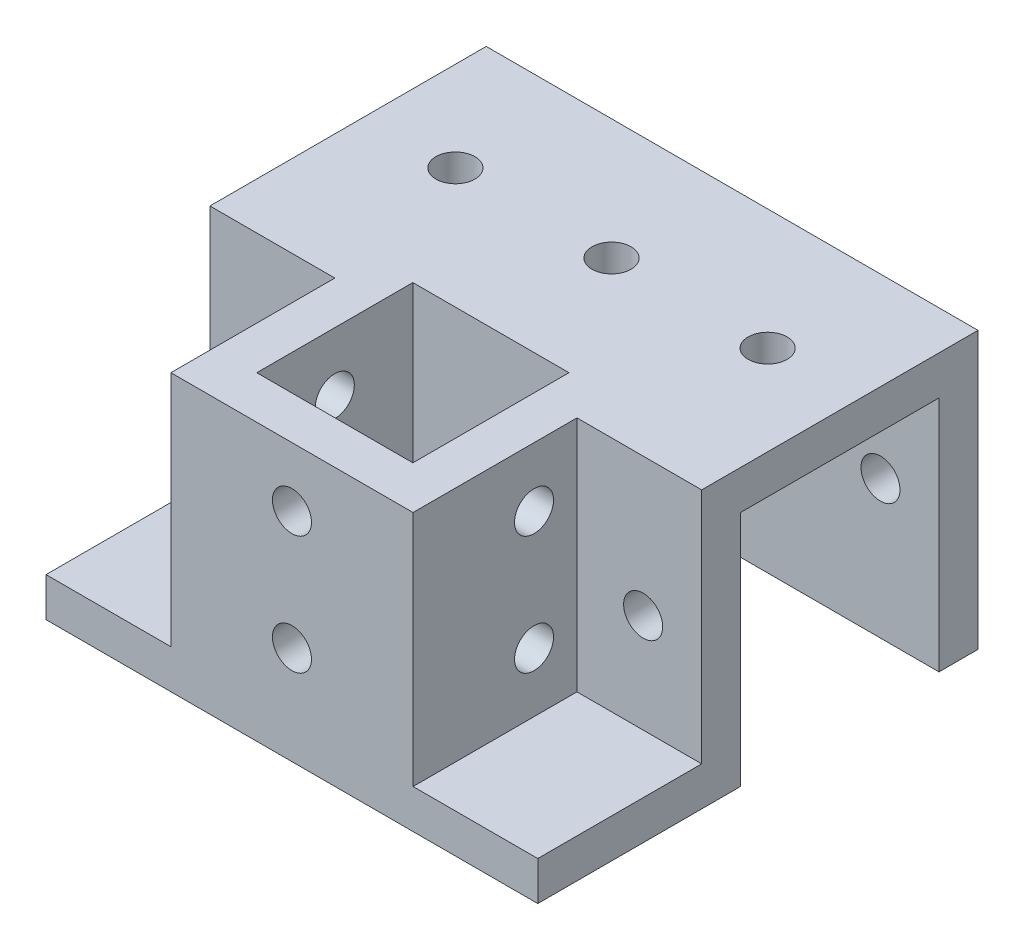
SolidWorks part; units mm, degrees
material "PLA"
ref_plane "Front Plane" through (0, 0, 0) normal (0, 0, 1) x (1, 0, 0)
ref_plane "Top Plane" through (0, 0, 0) normal (0, 1, 0) x (1, 0, 0)
ref_plane "Right Plane" through (0, 0, 0) normal (1, 0, 0) x (0, 0, -1)
sketch "Sketch2" plane through (0, 0, 0) normal (1, 0, 0) x (0, 0, -1)
  line L0 (-17.7, 17.7) -> (17.7, 17.7)
  line L1 (-12.7, 12.7) -> (12.7, 12.7)
  line L2 (-12.7, 12.7) -> (-12.7, -12.7)
  line L4 (12.7, 12.7) -> (12.7, -12.7)
  line L5 (-12.7, 12.7) -> (12.7, -12.7) construction
  line L6 (-12.7, -12.7) -> (12.7, 12.7) construction
  line L7 (17.7, 17.7) -> (17.7, -17.7)
  line L9 (-17.7, 17.7) -> (-17.7, -17.7)
  line L10 (-17.7, -17.7) -> (17.7, -17.7) construction
  line L11 (12.7, -12.7) -> (12.7, -17.7)
  line L12 (12.7, -17.7) -> (17.7, -17.7)
  line L13 (-12.7, -12.7) -> (-12.7, -17.7)
  line L14 (-12.7, -17.7) -> (-17.7, -17.7)
  line L16 (-12.7, -12.7) -> (12.7, -12.7) construction
  point P0 (0, 0)
  dimension "D1" = 25.4
  dimension "D2" = 25.4
  dimension "D3" = 5
extrude "Boss-Extrude1" add sketch "Sketch2" along normal blind 21
sketch "Sketch4" plane through (0, 0, 17.7) normal (0, 0, 1) x (1, 0, 0)
  line L0 (21, -17.7) -> (21, -12.7)
  line L1 (21, 17.7) -> (21, -17.7) construction
  line L2 (21, -12.7) -> (-21, -12.7)
  line L3 (21, -17.7) -> (-21, -17.7)
  line L4 (-21, -17.7) -> (-21, -12.7)
  dimension "D1" = 42
  dimension "D2" = 5
extrude "Boss-Extrude2" add sketch "Sketch4" along normal blind 21
sketch "Sketch5" plane through (0, 0, 17.7) normal (0, 0, -1) x (-1, 0, 0)
  line L0 (0, -17.7) -> (0, -12.7)
  line L1 (0, -12.7) -> (21, -12.7)
  line L2 (21, -12.7) -> (21, -17.7)
  line L3 (21, -17.7) -> (0, -17.7)
extrude "Boss-Extrude3" add sketch "Sketch5" along normal blind 5
sketch "Sketch7" plane through (0, 0, 17.7) normal (0, 0, 1) x (1, 0, 0)
  line L0 (0, 17.7) -> (5.0226, 17.7)
  line L1 (21, 17.7) -> (0, 17.7) construction
  line L2 (5.0226, 17.7) -> (5.0226, -12.7)
  line L3 (21, -12.7) -> (-21, -12.7) construction
  line L4 (5.0226, -12.7) -> (0, -12.7)
  line L5 (0, 17.7) -> (0, -12.7)
extrude "Boss-Extrude4" add sketch "Sketch7" along normal up to surface (21 mm away) up to face at (0, -15.2, 38.7)
sketch "Sketch8" plane through (-21, 0, 0) normal (-1, 0, 0) x (0, 0, 1)
  line L0 (12.7, -17.7) -> (12.7, 17.7)
  line L1 (-17.7, 17.7) -> (38.7, 17.7) construction
  line L2 (12.7, 17.7) -> (38.7, 17.7)
  line L3 (38.7, 17.7) -> (38.7, -17.7)
  line L4 (38.7, -17.7) -> (12.7, -17.7)
extrude "Boss-Extrude5" add sketch "Sketch8" along normal blind 5
sketch "Sketch9" plane through (-26, 0, 0) normal (-1, 0, 0) x (0, 0, 1)
  line L0 (12.7, -17.7) -> (12.7, -12.7)
  line L1 (12.7, 17.7) -> (12.7, -17.7) construction
  line L2 (12.7, -12.7) -> (38.7, -12.7)
  line L3 (38.7, -17.7) -> (38.7, 17.7) construction
  line L4 (38.7, -12.7) -> (38.7, -17.7)
  line L5 (38.7, -17.7) -> (12.7, -17.7)
  dimension "D1" = 5
extrude "Boss-Extrude6" add sketch "Sketch9" along normal blind 16 contours L5 L0 L2 L4
sketch "Sketch10" plane through (0, 0, 12.7) normal (0, 0, -1) x (-1, 0, 0)
  line L0 (26, 17.7) -> (42, 17.7)
  line L1 (26, 17.7) -> (26, -12.7)
  line L2 (42, -12.7) -> (42, 17.7)
  line L3 (26, -12.7) -> (42, -12.7)
extrude "Boss-Extrude7" add sketch "Sketch10" against normal blind 5 contours L3 L2 L0 L1
sketch "Sketch11" plane through (0, 0, 12.7) normal (0, 0, -1) x (-1, 0, 0)
  line L0 (21, 17.7) -> (21, 12.7)
  line L1 (21, 17.7) -> (21, -12.7) construction
  line L2 (21, 12.7) -> (42, 12.7)
  line L3 (42, -17.7) -> (42, 17.7) construction
  line L4 (42, 12.7) -> (42, 17.7)
  line L5 (42, 17.7) -> (21, 17.7)
  dimension "D1" = 5
extrude "Boss-Extrude9" add sketch "Sketch11" along normal blind 30.4
sketch "Sketch13" plane through (0, 12.7, 0) normal (0, -1, 0) x (1, 0, 0)
  line L0 (-21, -17.7) -> (-21, -12.7063)
  line L1 (-21, -17.7) -> (-21, 12.7) construction
  line L2 (-21, -12.7063) -> (-42, -12.7063)
  line L3 (-42, -17.7) -> (-42, 12.7) construction
  line L4 (-42, -12.7063) -> (-42, -17.7)
  line L5 (-42, -17.7) -> (-21, -17.7)
extrude "Boss-Extrude10" add sketch "Sketch13" along normal blind 30.4 contours L5 L0 L2 L4
sketch "Sketch15" plane through (-21, 0, 0) normal (1, 0, 0) x (0, 0, -1)
  line L0 (-12.7, 12.7) -> (-12.7, 17.7)
  line L1 (-38.7, 17.7) -> (17.7, 17.7) construction
  line L2 (-12.7, 17.7) -> (17.7, 17.7)
  line L3 (17.7, 17.7) -> (17.7, 12.7)
  line L4 (17.7, 17.7) -> (17.7, -17.7) construction
  line L5 (17.7, 12.7) -> (-12.7, 12.7)
extrude "Boss-Extrude11" add sketch "Sketch15" along normal up to surface (21 mm away) up to face at (0, 0, 5.25)
sketch "Sketch18" plane through (-21, 0, 0) normal (1, 0, 0) x (0, 0, -1)
  line L0 (-38.7, -12.7) -> (-12.7, -12.7) construction
  line L1 (-38.7, 17.7) -> (-33.7, 17.7)
  line L2 (-38.7, 17.7) -> (-38.7, -12.7)
  line L3 (-38.7, -12.7) -> (-33.7, -12.7)
  line L4 (-33.7, 17.7) -> (-33.7, -12.7)
  dimension "D1" = 5
extrude "Boss-Extrude12" add sketch "Sketch18" along normal up to surface (21 mm away) up to face at (0, 4.54, 23.1)
sketch "Sketch19" plane through (-21, 0, 0) normal (1, 0, 0) x (0, 0, -1)
  line L0 (12.7063, 12.7) -> (17.7, 12.7)
  line L1 (17.7, 12.7) -> (17.7, -17.7)
  line L2 (17.7, -17.7) -> (12.7063, -17.7)
  line L3 (12.7063, -17.7) -> (12.7063, 12.7)
extrude "Boss-Extrude13" add sketch "Sketch19" along normal up to surface (21 mm away) contours L3 L0 L1 L2 up to face at (0, -2.5, -15.2)
sketch "Sketch21" plane through (0, 17.7, 0) normal (0, 1, 0) x (1, 0, 0)
  line L0 (-20.5, -13.2) -> (-0.5, -13.2)
  line L1 (-21, -12.7) -> (0, -12.7)
  line L2 (-21, -12.7) -> (-21, -33.7)
  line L3 (-21, -33.7) -> (0, -33.7)
  line L4 (0, -12.7) -> (0, -33.7)
  line L5 (-0.5, -13.2) -> (-0.5, -33.2)
  line L6 (-20.5, -33.2) -> (-0.5, -33.2)
  line L7 (-20.5, -13.2) -> (-20.5, -33.2)
  dimension "D1" = 0.5
extrude "Boss-Extrude19" add sketch "Sketch21" against normal up to surface (30.4 mm away) contours L2 L1 L4 L3 | L0 L5 L6 L7 up to face at (13.0113, -12.7, 28.2)
sketch "Sketch22" plane through (5.0226, 0, 0) normal (1, 0, 0) x (0, 0, -1)
  line L0 (-38.7, 2.5) -> (-17.7, 2.5)
  line L1 (-38.7, 17.7) -> (-38.7, -12.7) construction
  line L2 (-17.7, 17.7) -> (-17.7, -12.7) construction
  line L3 (-38.7, 17.7) -> (-17.7, 17.7) construction
  circle A0 centre (-23.2, 10.1) radius 2.5
  circle A1 centre (-23.2, -5.1) radius 2.5
  dimension "D1" = 5
  dimension "D2" = 15.5
  dimension "D3" = 7.6
extrude "Cut-Extrude1" cut sketch "Sketch22" against normal up to surface (47.0226 mm away) contours A0 | A1
sketch "Sketch24" plane through (0, 0, 38.7) normal (0, 0, 1) x (1, 0, 0)
  line L1 (5.0226, -12.7) -> (5.0226, 17.7)
  line L2 (-26, 17.7) -> (5.0226, 17.7) construction
  line L3 (5.0226, 17.7) -> (5.0226, -12.7) construction
  circle A0 centre (-10.4887, -5.1) radius 2.5
  circle A1 centre (-10.4887, 10.1) radius 2.5
  dimension "D1" = 5
extrude "Cut-Extrude2" cut sketch "Sketch24" against normal up to surface (5.5 mm away) contours A1 | A0 up to face at (-10.5, 2.5, 33.2)
sketch "Sketch25" plane through (0, 17.7, 0) normal (0, 1, 0) x (1, 0, 0)
  circle A0 centre (-10.5, 2.25) radius 2.5
  circle A1 centre (-30.5, 2.25) radius 2.5
  circle A2 centre (9.5, 2.25) radius 2.5
  dimension "D1" = 5
  dimension "D2" = 2
  dimension "D3" = 2
extrude "Cut-Extrude3" cut sketch "Sketch25" against normal up to surface (5 mm away) contours A0 | A2 | A1 up to face at (-7, 12.7, -4.2354)
sketch "Sketch26" plane through (0, 0, -17.7) normal (0, 0, -1) x (-1, 0, 0)
  line L0 (42, -17.7) -> (42, 17.7) construction
  line L1 (-21, -17.7) -> (-21, 17.7) construction
  line L2 (-21, 0) -> (42, 0) construction
  circle A0 centre (-13.5, 0) radius 2.5
  circle A1 centre (34.5, 0) radius 2.5
  point P4 (-9.5, 0)
  point P8 (30.5, 0)
  point P9 (0, 0)
  point P10 (34.5, 0)
  point P11 (-20.5179, 4.7463)
  dimension "D1" = 5
  dimension "D2" = 7.5
  dimension "D3" = 7.5
extrude "Cut-Extrude4" cut sketch "Sketch26" against normal through all contours A0 | A1
sketch "Sketch28" plane through (0, 0, -12.7) normal (0, 0, 1) x (1, 0, 0)
  line L1 (0, 12.7) -> (21, 12.7)
  line L2 (0, 12.7) -> (0, -17.7)
  line L3 (0, -17.7) -> (21, -17.7)
  line L4 (21, 12.7) -> (21, -17.7)
extrude "Cut-Extrude5" cut sketch "Sketch28" against normal up to surface (0.0063 mm away) up to face at (-34.5, 2.5, -12.7063)
